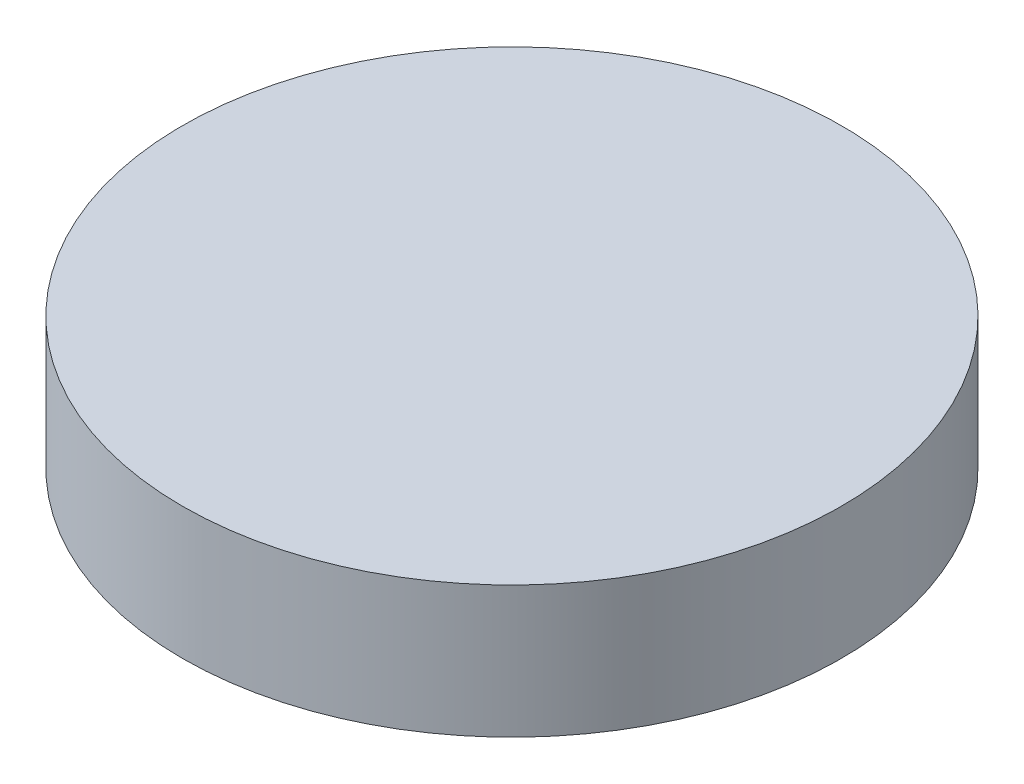
SolidWorks part; units mm, degrees
ref_plane "Front Plane" through (0, 0, 0) normal (0, 0, 1) x (1, 0, 0)
ref_plane "Top Plane" through (0, 0, 0) normal (0, 1, 0) x (1, 0, 0)
ref_plane "Right Plane" through (0, 0, 0) normal (1, 0, 0) x (0, 0, -1)
sketch "Sketch1" plane through (0, 0, 0) normal (0, 1, 0) x (1, 0, 0)
  circle A0 centre (0, 0) radius 63.5
  dimension "D1" = 127
extrude "Boss-Extrude1" add sketch "Sketch1" along normal blind 25.4
